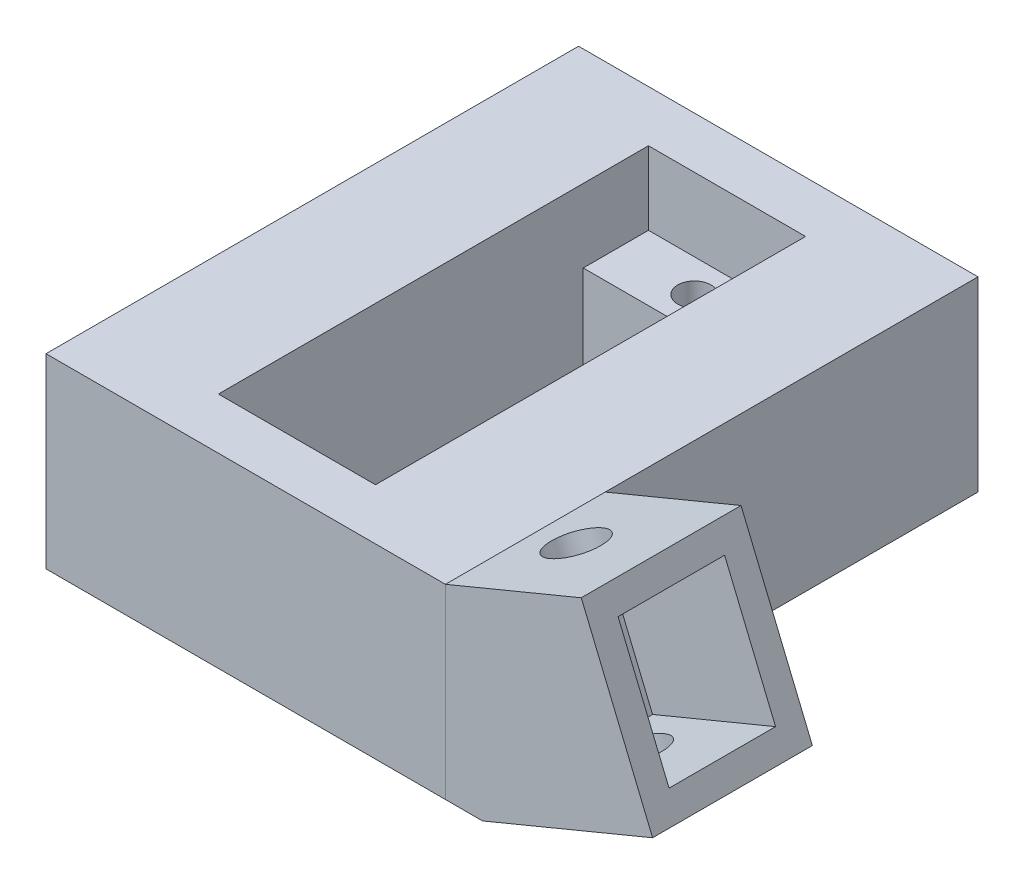
SolidWorks part; units mm, degrees
ref_plane "Front Plane" through (0, 0, 0) normal (0, 0, 1) x (1, 0, 0)
ref_plane "Top Plane" through (0, 0, 0) normal (0, 1, 0) x (1, 0, 0)
ref_plane "Right Plane" through (0, 0, 0) normal (1, 0, 0) x (0, 0, -1)
sketch "Sketch1" plane through (0, 0, 0) normal (0, 0, 1) x (1, 0, 0)
  line L1 (8.671, 9.0036) -> (-11.329, 9.0036)
  line L3 (11.4585, -4.9953) -> (8.671, -4.9953)
  line L5 (-11.329, -4.9953) -> (8.671, -4.9953)
  line L9 (8.671, 9.0036) -> (8.671, -4.9953)
  line L15 (-11.329, 9.0036) -> (-21.329, 9.0036)
  line L17 (-21.329, 9.0036) -> (-21.329, -4.9953)
  line L18 (-21.329, -4.9953) -> (-11.329, -4.9953)
  line L25 (18.8739, 13.2298) -> (8.671, 9.0036)
  line L26 (20.7873, 8.6104) -> (18.8739, 13.2298)
  line L27 (24.2314, 0.2955) -> (11.4585, -4.9953)
  line L28 (20.7873, 8.6104) -> (24.2314, 0.2955)
  dimension "D1" = 20
extrude "Boss-Extrude1" add sketch "Sketch1" along normal blind 40 contours L1 L15 L17 L18 L5 L9
sketch "Sketch3" plane through (0, 9.0036, 0) normal (0, 1, 0) x (1, 0, 0)
  line L0 (-6.329, -40) -> (-6.329, 0) construction
  line L1 (8.671, -40) -> (-21.329, -40) construction
  line L2 (-11.329, 0) -> (8.671, 0) construction
  line L3 (-21.329, -20) -> (8.671, -20) construction
  line L4 (-21.329, -40) -> (-21.329, 0) construction
  line L5 (8.671, -40) -> (8.671, 0) construction
  line L6 (-12.229, -31.25) -> (-0.429, -31.25)
  line L8 (-12.229, -3.85) -> (-12.229, -36.15)
  line L9 (-12.229, -36.15) -> (-0.429, -36.15)
  line L10 (-0.429, -3.85) -> (-0.429, -36.15)
  line L11 (-6.329, -31.25) -> (-6.329, -36.15) construction
  line L12 (-12.229, -3.85) -> (-0.429, -3.85)
  line L13 (-12.229, -8.75) -> (-0.429, -8.75)
  circle A0 centre (-6.329, -33.7) radius 1.25
  circle A1 centre (-6.329, -6.3) radius 1.25
  point P24 (-0.429, -20)
  point P26 (-12.229, -20)
  dimension "D1" = 11.8
  dimension "D2" = 5.9
  dimension "D3" = 16.15
  dimension "D4" = 4.9
sketch "Sketch4" plane through (0, 9.0036, 0) normal (0, 1, 0) x (1, 0, 0)
  line L0 (-12.229, -36.15) -> (-0.429, -36.15) construction
  line L1 (-0.429, -3.85) -> (-0.429, -36.15) construction
  line L2 (-12.229, -3.85) -> (-0.429, -3.85) construction
  line L3 (-12.229, -3.85) -> (-12.229, -36.15) construction
  line L4 (-12.229, -36.15) -> (-0.429, -36.15)
  line L5 (-0.429, -3.85) -> (-0.429, -36.15)
  line L6 (-12.229, -3.85) -> (-0.429, -3.85)
  line L7 (-12.229, -3.85) -> (-12.229, -36.15)
extrude "Cut-Extrude1" cut sketch "Sketch4" against normal blind 5.5
sketch "Sketch5" plane through (0, 3.5036, 0) normal (0, 1, 0) x (1, 0, 0)
  line L0 (-12.229, -31.25) -> (-0.429, -31.25) construction
  line L1 (-0.429, -3.85) -> (-0.429, -36.15) construction
  line L2 (-12.229, -3.85) -> (-12.229, -36.15) construction
  line L3 (-12.229, -8.75) -> (-0.429, -8.75) construction
  line L4 (-12.229, -31.25) -> (-0.429, -31.25)
  line L5 (-0.429, -8.75) -> (-0.429, -31.25)
  line L6 (-12.229, -8.75) -> (-12.229, -31.25)
  line L7 (-12.229, -8.75) -> (-0.429, -8.75)
extrude "Cut-Extrude2" cut sketch "Sketch5" against normal through all
sketch "Sketch6" plane through (0, 3.5036, 0) normal (0, 1, 0) x (1, 0, 0)
  circle A0 centre (-6.329, -6.3) radius 1.25
  circle A1 centre (-6.329, -33.7) radius 1.25
extrude "Cut-Extrude3" cut sketch "Sketch6" against normal through all
sketch "Sketch7" plane through (0, 0, 40) normal (0, 0, 1) x (1, 0, 0)
  line L0 (20.7873, 8.6104) -> (18.8739, 13.2298) construction
  line L1 (20.7873, 8.6104) -> (24.2314, 0.2955) construction
  line L2 (24.2314, 0.2955) -> (11.4585, -4.9953) construction
  line L3 (11.4585, -4.9953) -> (8.671, -4.9953) construction
  line L4 (8.671, 9.0036) -> (8.671, -4.9953) construction
  line L5 (18.8739, 13.2298) -> (8.671, 9.0036) construction
  line L6 (20.7873, 8.6104) -> (18.8739, 13.2298)
  line L7 (20.7873, 8.6104) -> (24.2314, 0.2955)
  line L8 (24.2314, 0.2955) -> (11.4585, -4.9953)
  line L9 (11.4585, -4.9953) -> (8.671, -4.9953)
  line L10 (8.671, 9.0036) -> (8.671, -4.9953)
  line L11 (18.8739, 13.2298) -> (8.671, 9.0036)
extrude "Boss-Extrude2" add sketch "Sketch7" against normal blind 12 separate body
sketch "Sketch8" plane through (3.4442, -8.3149, 0) normal (0.3827, -0.9239, 0) x (0.9239, 0.3827, 0)
  line L0 (8.6747, 34) -> (22.5, 34) construction
  line L1 (8.6747, 28) -> (8.6747, 40) construction
  line L2 (22.5, 28) -> (22.5, 40) construction
  line L3 (15.5873, 28) -> (15.5873, 40) construction
  line L4 (8.6747, 28) -> (22.5, 28) construction
  line L5 (8.6747, 40) -> (22.5, 40) construction
  circle A0 centre (15.5873, 34) radius 2
extrude "Cut-Extrude4" cut sketch "Sketch8" against normal through all
sketch "Sketch9" plane through (20.7873, 8.6104, 0) normal (0.9239, 0.3827, 0) x (0, 0, -1)
  line L0 (-28, -9) -> (-40, -9) construction
  line L1 (-30, -7) -> (-38, -7)
  line L2 (-30, -7) -> (-30, 3)
  line L3 (-30, 3) -> (-38, 3)
  line L4 (-38, -7) -> (-38, 3)
  line L5 (-40, -9) -> (-40, 5) construction
  line L6 (-28, 5) -> (-40, 5) construction
  line L7 (-28, -9) -> (-28, 5) construction
  dimension "D1" = 2
  dimension "D2" = 2
  dimension "D3" = 2
  dimension "D4" = 2
extrude "Cut-Extrude5" cut sketch "Sketch9" against normal blind 10
